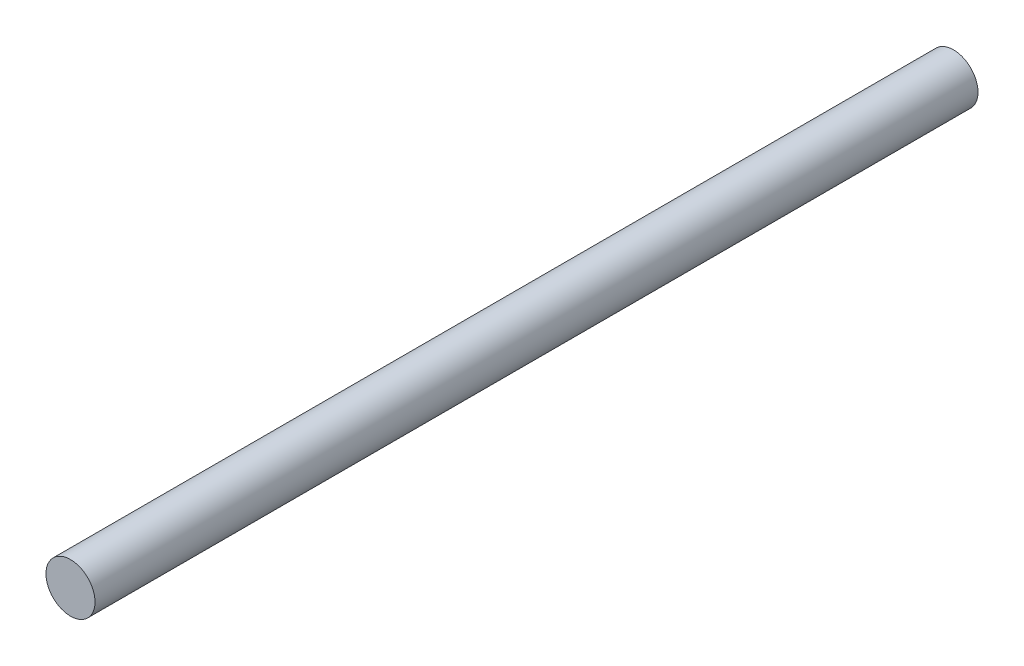
SolidWorks part; units mm, degrees
ref_plane "Front Plane" through (0, 0, 0) normal (0, 0, 1) x (1, 0, 0)
ref_plane "Top Plane" through (0, 0, 0) normal (0, 1, 0) x (1, 0, 0)
ref_plane "Right Plane" through (0, 0, 0) normal (1, 0, 0) x (0, 0, -1)
sketch "Sketch1" plane through (0, 0, 0) normal (0, 0, 1) x (1, 0, 0)
  line L1 (-25.4, 0) -> (25.4, 0) construction
  dimension "OD" = 50.8
sketch "Sketch2" plane through (0, 0, 0) normal (1, 0, 0) x (0, 0, -1)
  line L0 (457.2, 0) -> (-457.2, 0)
  point P4 (0, 0)
  dimension "Length" = 914.4
sketch "Sketch3" plane through (0, 0, 0) normal (0, 0, 1) x (1, 0, 0)
  circle A0 centre (0, 0) radius 25.4
extrude "Boss-Extrude1" add sketch "Sketch3" along normal up to vertex (457.2 mm away) and the other way up to vertex (457.2 mm away) up to point (0, 0, 457.2) other way up to point (0, 0, -457.2)
